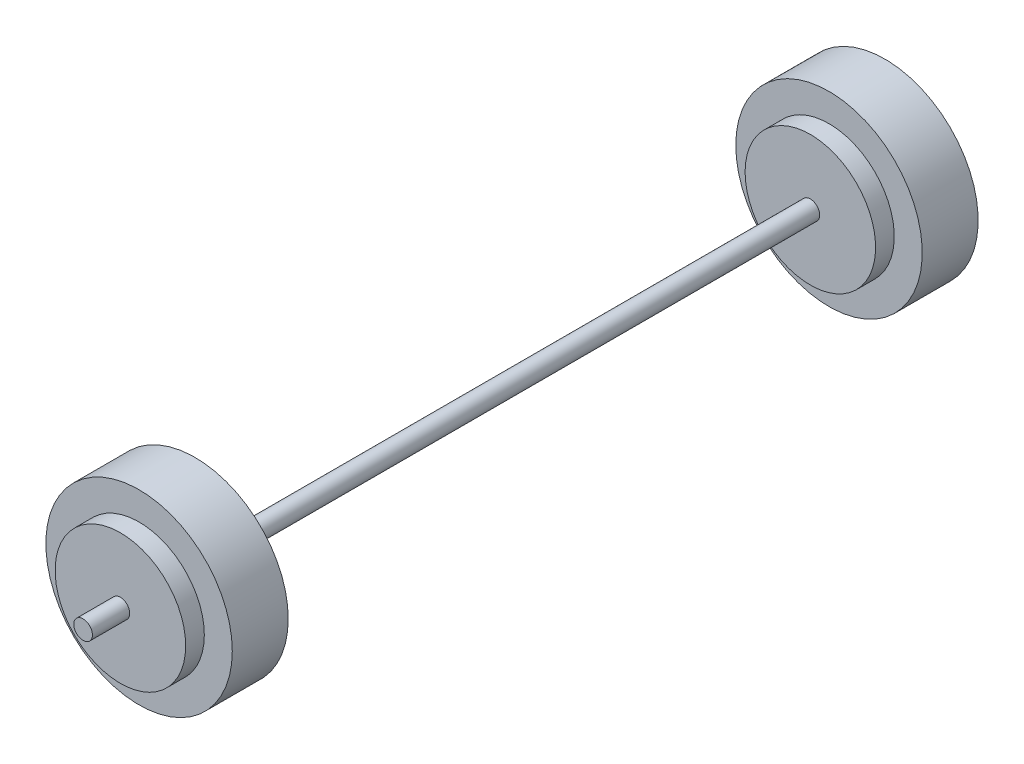
SolidWorks part; units mm, degrees
ref_plane "Front Plane" through (0, 0, 0) normal (0, 0, 1) x (1, 0, 0)
ref_plane "Top Plane" through (0, 0, 0) normal (0, 1, 0) x (1, 0, 0)
ref_plane "Right Plane" through (0, 0, 0) normal (1, 0, 0) x (0, 0, -1)
sketch "Sketch1" plane through (0, 0, 0) normal (0, 0, 1) x (1, 0, 0)
  circle A0 centre (0, 0) radius 127
  dimension "D1" = 254
extrude "Boss-Extrude1" add sketch "Sketch1" against normal blind 76.2
sketch "Sketch2" plane through (0, 0, 0) normal (0, 0, 1) x (1, 0, 0)
  circle A0 centre (0, 0) radius 88.9
  circle A1 centre (0, 0) radius 127 construction
  dimension "D1" = 177.8
  dimension "D2" = 38.1
extrude "Boss-Extrude2" add sketch "Sketch2" along normal blind 25.4
sketch "Sketch3" plane through (0, 0, 25.4) normal (0, 0, 1) x (1, 0, 0)
  circle A0 centre (0, 0) radius 12.7
  dimension "D1" = 25.4
extrude "Boss-Extrude3" add sketch "Sketch3" along normal blind 50.8
sketch "Sketch4" plane through (0, 0, -76.2) normal (0, 0, -1) x (-1, 0, 0)
  circle A0 centre (0, 0) radius 88.9
  dimension "D1" = 177.8
extrude "Boss-Extrude4" add sketch "Sketch4" along normal blind 25.4
sketch "Sketch6" plane through (0, 0, -101.6) normal (0, 0, -1) x (-1, 0, 0)
  circle A0 centre (0, 0) radius 12.7
  dimension "D1" = 25.4
extrude "Boss-Extrude5" add sketch "Sketch6" along normal blind 812.8
sketch "Sketch7" plane through (0, 0, -914.4) normal (0, 0, -1) x (-1, 0, 0)
  circle A0 centre (0, 0) radius 88.9
  dimension "D1" = 177.8
extrude "Boss-Extrude6" add sketch "Sketch7" along normal blind 25.4
sketch "Sketch8" plane through (0, 0, -939.8) normal (0, 0, -1) x (-1, 0, 0)
  circle A0 centre (0, 0) radius 127
extrude "Boss-Extrude7" add sketch "Sketch8" along normal blind 76.2
sketch "Sketch9" plane through (0, 0, -1016) normal (0, 0, -1) x (-1, 0, 0)
  circle A0 centre (0, 0) radius 88.9
  dimension "D1" = 177.8
extrude "Boss-Extrude8" add sketch "Sketch9" along normal blind 25.4
sketch "Sketch10" plane through (0, 0, -1041.4) normal (0, 0, -1) x (-1, 0, 0)
  circle A0 centre (0, 0) radius 12.7
  dimension "D1" = 25.4
extrude "Boss-Extrude9" add sketch "Sketch10" along normal blind 50.8
